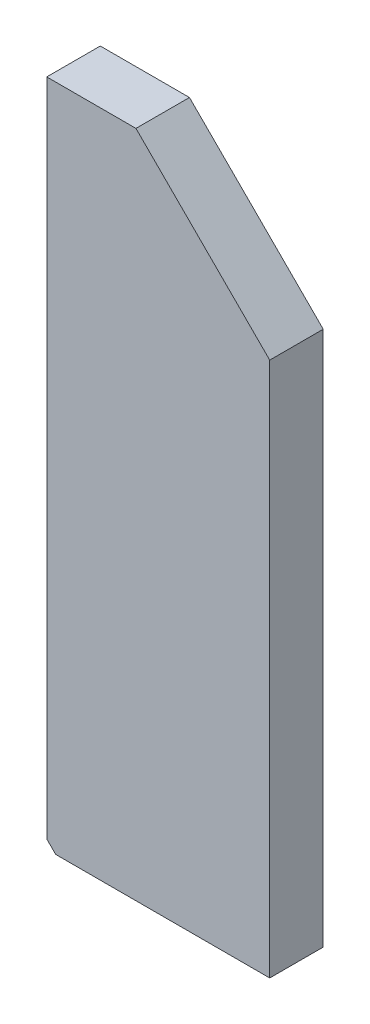
SolidWorks part; units mm, degrees
ref_plane "Front Plane" through (0, 0, 0) normal (0, 0, 1) x (1, 0, 0)
ref_plane "Top Plane" through (0, 0, 0) normal (0, 1, 0) x (1, 0, 0)
ref_plane "Right Plane" through (0, 0, 0) normal (1, 0, 0) x (0, 0, -1)
sketch "Sketch1" plane through (0, 0, 0) normal (0, 0, 1) x (1, 0, 0)
  line L1 (-52.5, 113.2812) -> (-2.5, 113.2812)
  line L2 (-52.5, 113.2812) -> (-52.5, -36.7188)
  line L3 (-52.5, -36.7188) -> (-2.5, -36.7188)
  line L4 (-2.5, 113.2812) -> (-2.5, -36.7188)
  line L5 (-52.5, 113.2812) -> (-2.5, -36.7188) construction
  line L6 (-52.5, -36.7188) -> (-2.5, 113.2812) construction
  point P0 (-27.5, 38.2812)
  dimension "D1" = 150
  dimension "D2" = 50
extrude "Boss-Extrude1" add sketch "Sketch1" along normal blind 12
hole_wizard "M5 Tapped Hole1" positions "Sketch2" profile "Sketch3" tap size "M5" standard "ISO"
sketch "Sketch2" plane through (-52.5, 0, 0) normal (-1, 0, 0) x (0, 0, 1)
  line L0 (12, -36.7188) -> (0, -36.7188) construction
  line L2 (12, 113.2812) -> (0, 113.2812) construction
  point P0 (6, 98.2812)
  point P2 (6, 43.2812)
  point P4 (6, -11.7188)
  point P10 (6, -36.7188)
  dimension "D1" = 15
  dimension "D2" = 80
  dimension "D3" = 25
sketch "Sketch3" plane through (-52.5, 98.2812, 6) normal (0, 1, 0) x (0, 0, 1)
  line L0 (0, 0) -> (0, 11.2618)
  line L1 (0, 11.2618) -> (2.1, 10)
  line L2 (2.1, 10) -> (2.1, 0)
  line L5 (2.1, 0) -> (0, 0)
  line L10 (0, 11.2618) -> (-2.1, 10) construction
  line L11 (0, -6.35) -> (0, 107.95) construction
  dimension "Tap Drill Dia." = 4.2
  dimension "Tap Drill Depth" = 10
  dimension "Drill Angle" = 118
cosmetic thread "Hole Thread1"
cosmetic thread "Hole Thread2"
cosmetic thread "Hole Thread3"
hole_wizard "M5 Tapped Hole2" positions "Sketch4" profile "Sketch5" tap size "M5" standard "ISO"
sketch "Sketch4" plane through (0, -36.7188, 0) normal (0, -1, 0) x (-1, 0, 0)
  line L0 (52.5, -12) -> (52.5, 0) construction
  line L1 (52.5, -12) -> (2.5, -12) construction
  point P0 (46.5, -6)
  point P2 (8.5, -6)
  dimension "D1" = 6
  dimension "D2" = 44
  dimension "D3" = 6
  dimension "D4" = 6
sketch "Sketch5" plane through (-46.5, -36.7188, 6) normal (1, 0, 0) x (0, 0, -1)
  line L0 (0, 0) -> (0, 11.2618)
  line L1 (0, 11.2618) -> (2.1, 10)
  line L2 (2.1, 10) -> (2.1, 0)
  line L5 (2.1, 0) -> (0, 0)
  line L10 (0, 11.2618) -> (-2.1, 10) construction
  line L11 (0, -6.35) -> (0, 107.95) construction
  dimension "Tap Drill Dia." = 4.2
  dimension "Tap Drill Depth" = 10
  dimension "Drill Angle" = 118
cosmetic thread "Hole Thread4"
cosmetic thread "Hole Thread5"
chamfer "Chamfer1" distance 30 angle 45 1 edges at (-2.5, 113.2812, 6)
chamfer "Chamfer2" distance 2 angle 45 1 edges at (-52.5, -36.7188, 6)
